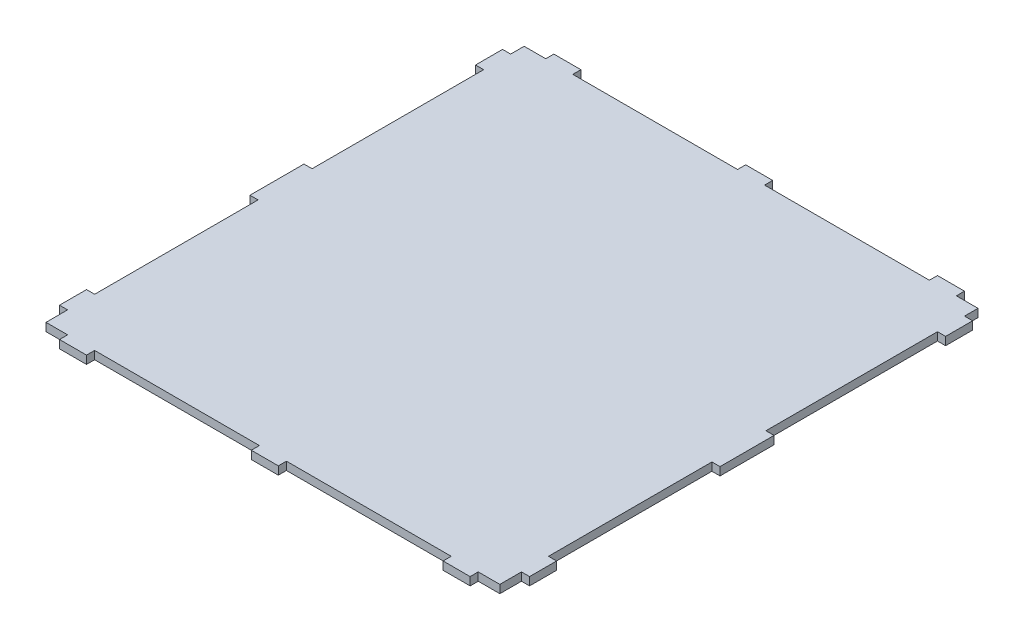
SolidWorks part; units mm, degrees
ref_plane "Front Plane" through (0, 0, 0) normal (0, 0, 1) x (1, 0, 0)
ref_plane "Top Plane" through (0, 0, 0) normal (0, 1, 0) x (1, 0, 0)
ref_plane "Right Plane" through (0, 0, 0) normal (1, 0, 0) x (0, 0, -1)
sketch "Sketch1" plane through (0, 0, 0) normal (0, 1, 0) x (1, 0, 0)
  line L0 (-114.6009, -60.5) -> (-114.6009, 0)
  line L3 (-114.6009, -78.5) -> (56.3991, -78.5) construction
  line L4 (56.3991, 98.5) -> (56.3991, -78.5) construction
  line L5 (53.3991, 98.5) -> (53.3991, 93.5) construction
  line L6 (53.3991, 93.5) -> (56.3991, 93.5)
  line L9 (-117.6009, 93.5) -> (-117.6009, 83.5)
  line L10 (-117.6009, 83.5) -> (-114.6009, 83.5)
  line L11 (-114.6009, 93.5) -> (-114.6009, 98.5)
  line L12 (-114.6009, -70.5) -> (-117.6009, -70.5)
  line L13 (-117.6009, -70.5) -> (-117.6009, -60.5)
  line L14 (-117.6009, -60.5) -> (-114.6009, -60.5)
  line L15 (-114.6009, -70.5) -> (-114.6009, -78.5)
  line L16 (-114.6009, 20) -> (-117.6009, 20)
  line L17 (-117.6009, 20) -> (-117.6009, 0)
  line L18 (-117.6009, 0) -> (-114.6009, 0)
  line L19 (-114.6009, 20) -> (-114.6009, 83.5)
  line L20 (-117.6009, 10) -> (56.3991, 10) construction
  line L21 (53.3991, -78.5) -> (53.3991, 98.5) construction
  line L22 (56.3991, 93.5) -> (56.3991, 83.5)
  line L23 (56.3991, 83.5) -> (53.3991, 83.5)
  line L24 (53.3991, 83.5) -> (53.3991, 20)
  line L25 (53.3991, 20) -> (56.3991, 20)
  line L26 (56.3991, 20) -> (56.3991, 0)
  line L27 (56.3991, 0) -> (53.3991, 0)
  line L28 (53.3991, 0) -> (53.3991, -60.5)
  line L29 (53.3991, -60.5) -> (56.3991, -60.5)
  line L30 (56.3991, -60.5) -> (56.3991, -70.5)
  line L31 (56.3991, -70.5) -> (53.3991, -70.5)
  line L32 (53.3991, -70.5) -> (53.3991, -78.5)
  line L33 (-114.6009, 98.5) -> (-106.6009, 98.5)
  line L34 (-106.6009, 98.5) -> (-106.6009, 101.5)
  line L35 (-106.6009, 101.5) -> (-96.6009, 101.5)
  line L36 (-96.6009, 101.5) -> (-96.6009, 98.5)
  line L37 (-96.6009, 98.5) -> (-35.6009, 98.5)
  line L38 (-35.6009, 98.5) -> (-35.6009, 101.5)
  line L39 (-35.6009, 101.5) -> (-25.6009, 101.5)
  line L40 (-25.6009, 101.5) -> (-25.6009, 98.5)
  line L41 (-25.6009, 98.5) -> (35.3991, 98.5)
  line L42 (-114.6009, -78.5) -> (-106.6009, -78.5)
  line L43 (-106.6009, -78.5) -> (-106.6009, -81.5)
  line L44 (-106.6009, -81.5) -> (-96.6009, -81.5)
  line L45 (-96.6009, -81.5) -> (-96.6009, -78.5)
  line L47 (35.3991, -78.5) -> (35.3991, -81.5)
  line L48 (35.3991, -81.5) -> (45.3991, -81.5)
  line L49 (45.3991, -81.5) -> (45.3991, -78.5)
  line L50 (45.3991, -78.5) -> (53.3991, -78.5)
  line L51 (53.3991, 98.5) -> (53.3991, 93.5)
  line L52 (45.3991, 98.5) -> (45.3991, 101.5)
  line L53 (45.3991, 101.5) -> (35.3991, 101.5)
  line L54 (35.3991, 101.5) -> (35.3991, 98.5)
  line L55 (45.3991, 98.5) -> (53.3991, 98.5)
  line L58 (-35.6009, -78.5) -> (-35.6009, -81.5)
  line L59 (-35.6009, -81.5) -> (-25.6009, -81.5)
  line L60 (-25.6009, -81.5) -> (-25.6009, -78.5)
  line L61 (-96.6009, -78.5) -> (-35.6009, -78.5)
  line L62 (-25.6009, -78.5) -> (35.3991, -78.5)
  line L63 (-30.6009, -81.5) -> (-30.6009, -84.0658) construction
  line L64 (-114.6009, 93.5) -> (-117.6009, 93.5)
  dimension "D1" = 8
  dimension "D2" = 3
  dimension "D3" = 3
  dimension "D4" = 10
  dimension "D5" = 10
  dimension "D6" = 8
  dimension "D7" = 5
  dimension "D8" = 20
  dimension "D9" = 10
  dimension "D10" = 10
  dimension "D11" = 174
  dimension "D12" = 8
  dimension "D13" = 10
  dimension "D14" = 8
  dimension "D15" = 10
  dimension "D16" = 3
  dimension "D17" = 3
  dimension "D18" = 5
  dimension "D19" = 10
  dimension "D20" = 20
  dimension "D21" = 3
  dimension "D22" = 10
  dimension "D23" = 8
  dimension "D24" = 8
  dimension "D25" = 3
  dimension "D26" = 3
  dimension "D27" = 3
  dimension "D28" = 10
  dimension "D29" = 10
  dimension "D30" = 3
  dimension "D31" = 60.5
  dimension "D32" = 3
  dimension "D33" = 63.5
  dimension "D34" = 10
  dimension "D35" = 3
  dimension "D36" = 3
  dimension "D37" = 3
  dimension "D38" = 61
  dimension "D39" = 61
  dimension "D40" = 61
  dimension "D41" = 61
  dimension "D42" = 3
  dimension "D43" = 3
extrude "Boss-Extrude1" add sketch "Sketch1" along normal blind 3
